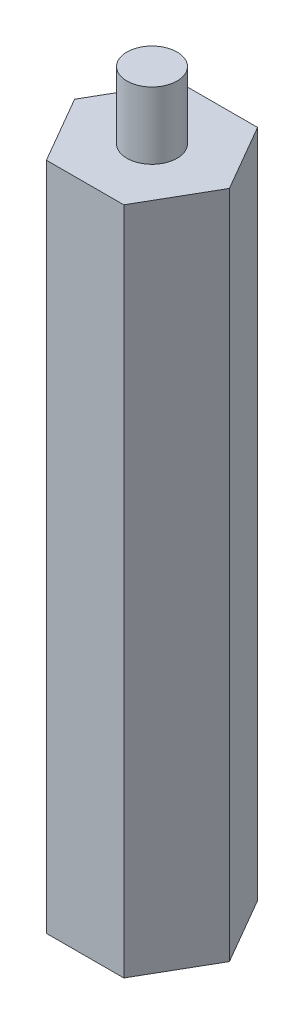
SolidWorks part; units mm, degrees
ref_plane "前视基准面" through (0, 0, 0) normal (0, 0, 1) x (1, 0, 0)
ref_plane "上视基准面" through (0, 0, 0) normal (0, 1, 0) x (1, 0, 0)
ref_plane "右视基准面" through (0, 0, 0) normal (1, 0, 0) x (0, 0, -1)
sketch "草图1" plane through (0, 0, 0) normal (0, 1, 0) x (1, 0, 0)
  line L1 (4.6107, 8.0047) -> (-4.6269, 7.9953)
  line L2 (-4.6269, 7.9953) -> (-9.2376, -0.0094)
  line L3 (-9.2376, -0.0094) -> (-4.6107, -8.0047)
  line L4 (-4.6107, -8.0047) -> (4.6269, -7.9953)
  line L5 (4.6269, -7.9953) -> (9.2376, 0.0094)
  line L6 (9.2376, 0.0094) -> (4.6107, 8.0047)
  circle A0 centre (0, 0) radius 8 construction
extrude "凸台-拉伸1" add sketch "草图1" along normal blind 80
sketch "草图2" plane through (0, 80, 0) normal (0, 1, 0) x (1, 0, 0)
  circle A0 centre (0, 0) radius 3
extrude "凸台-拉伸2" add sketch "草图2" along normal blind 8 contours A0
sketch "草图3" plane through (0, 0, 0) normal (0, -1, 0) x (1, 0, 0)
  circle A0 centre (0, 0) radius 3
extrude "切除-拉伸1" cut sketch "草图3" against normal blind 8
